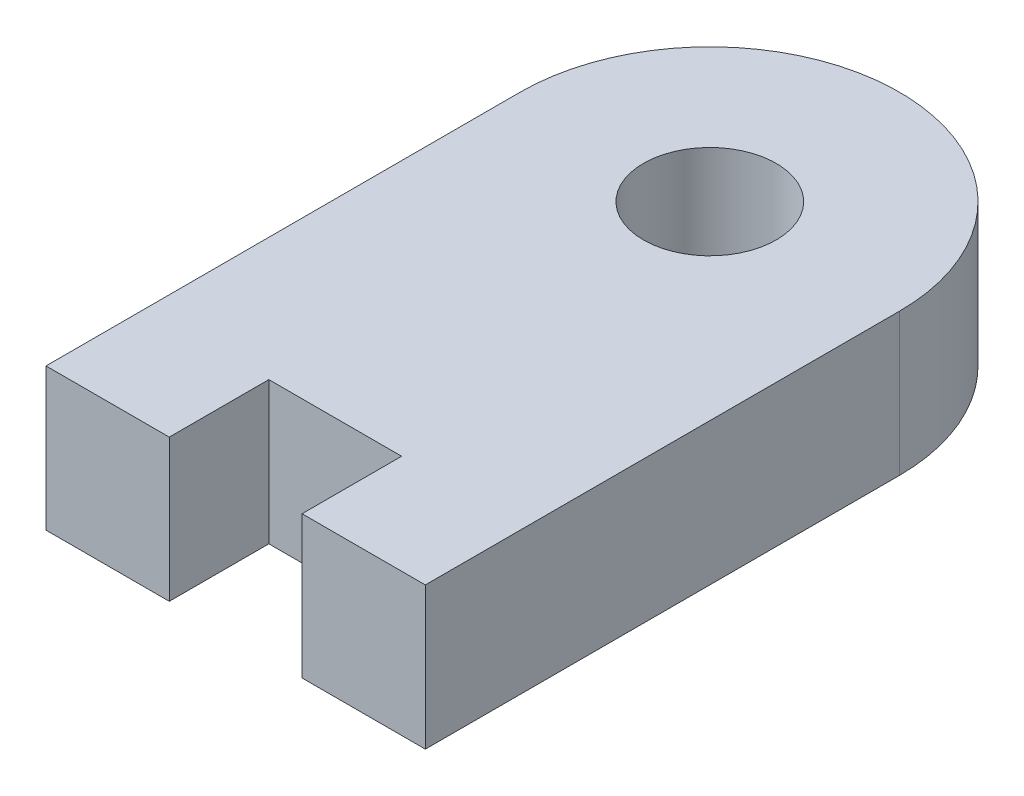
SolidWorks part; units mm, degrees
ref_plane "Front Plane" through (0, 0, 0) normal (0, 0, 1) x (1, 0, 0)
ref_plane "Top Plane" through (0, 0, 0) normal (0, 1, 0) x (1, 0, 0)
ref_plane "Right Plane" through (0, 0, 0) normal (1, 0, 0) x (0, 0, -1)
sketch "Sketch1" plane through (0, 0, 0) normal (0, 1, 0) x (1, 0, 0)
  line L0 (-4, 0) -> (-4, -10)
  line L1 (4, 0) -> (4, -10)
  line L2 (4, -10) -> (1.4, -10)
  line L3 (-1.4, -10) -> (-1.4, -7.9)
  line L4 (-1.4, -7.9) -> (1.4, -7.9)
  line L5 (0, 0) -> (0, -11.3756) construction
  line L6 (1.4, -10) -> (1.4, -7.9)
  line L7 (-1.4, -10) -> (-4, -10)
  arc A0 (4, 0) -> (-4, 0) centre (0, 0) ccw
  circle A1 centre (0, 0) radius 1.4
  point P13 (0, -7.9)
  dimension "D1" = 8
  dimension "D2" = 2.8
  dimension "D3" = 10
  dimension "D4" = 2.1
  dimension "D5" = 2.8
extrude "Boss-Extrude1" add sketch "Sketch1" along normal blind 3
